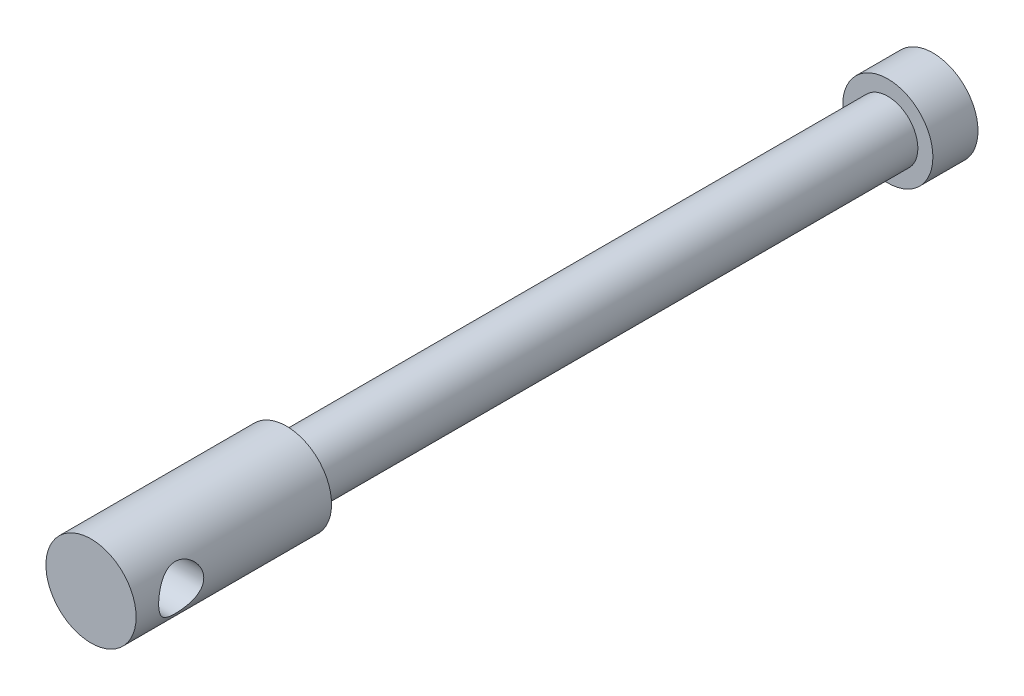
SolidWorks part; units mm, degrees
ref_plane "前基準面" through (0, 0, 0) normal (0, 0, 1) x (1, 0, 0)
ref_plane "上基準面" through (0, 0, 0) normal (0, 1, 0) x (1, 0, 0)
ref_plane "右基準面" through (0, 0, 0) normal (1, 0, 0) x (0, 0, -1)
sketch "草圖1" plane through (0, 0, 0) normal (1, 0, 0) x (0, 0, -1)
  line L0 (-17.8043, 0) -> (48.3913, 0) construction
  line L1 (0, 2) -> (0, 3)
  line L2 (0, 3) -> (-13, 3)
  line L3 (-13, 3) -> (-13, 0)
  line L4 (0, 2) -> (40, 2)
  line L5 (40, 2) -> (40, 3)
  line L6 (40, 3) -> (43, 3)
  line L7 (43, 3) -> (43, 0)
  line L8 (-13, 0) -> (43, 0)
  dimension "D1" = 3
  dimension "D2" = 13
  dimension "D3" = 6
  dimension "D4" = 4
  dimension "D5" = 40
revolve "旋轉1" add sketch "草圖1" angle 360 about L0
sketch "草圖2" plane through (0, 0, 0) normal (1, 0, 0) x (0, 0, -1)
  line L0 (-13, 3) -> (-13, -3) construction
  circle A0 centre (-10, 0) radius 1.5
  dimension "D1" = 3
  dimension "D2" = 3
extrude "除料-伸長1" cut sketch "草圖2" against normal through all both and the other way through all
